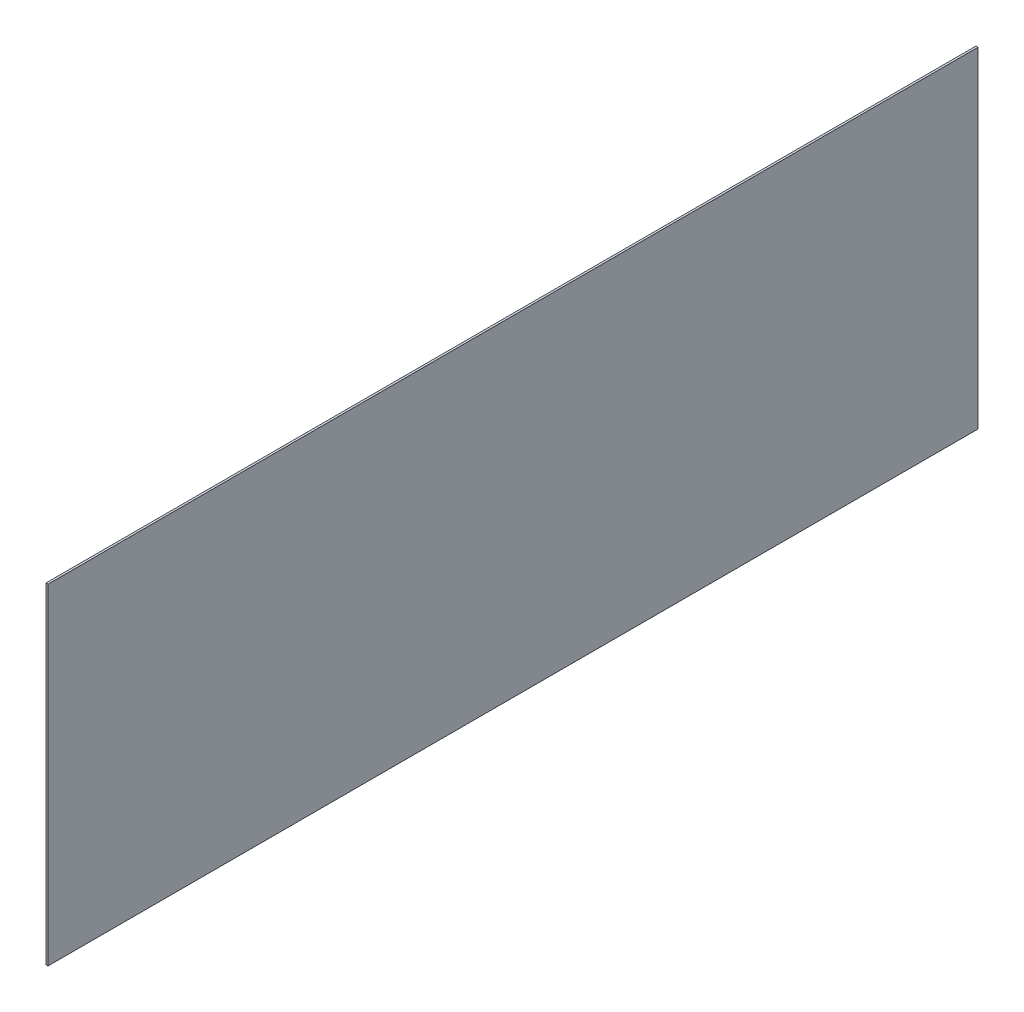
SolidWorks part; units mm, degrees
material "1023 Carbon Steel Sheet (SS)"
ref_plane "Front Plane" through (0, 0, 0) normal (0, 0, 1) x (1, 0, 0)
ref_plane "Top Plane" through (0, 0, 0) normal (0, 1, 0) x (1, 0, 0)
ref_plane "Right Plane" through (0, 0, 0) normal (1, 0, 0) x (0, 0, -1)
sketch "Sketch1" plane through (0, 0, 0) normal (1, 0, 0) x (0, 0, -1)
  line L1 (-225, 80) -> (225, 80)
  line L2 (-225, 80) -> (-225, -80)
  line L3 (-225, -80) -> (225, -80)
  line L4 (225, 80) -> (225, -80)
  line L5 (-225, 80) -> (225, -80) construction
  line L6 (-225, -80) -> (225, 80) construction
  point P0 (0, 0)
  dimension "D1" = 450
  dimension "D2" = 160
extrude "Boss-Extrude1" add sketch "Sketch1" along normal blind 1
